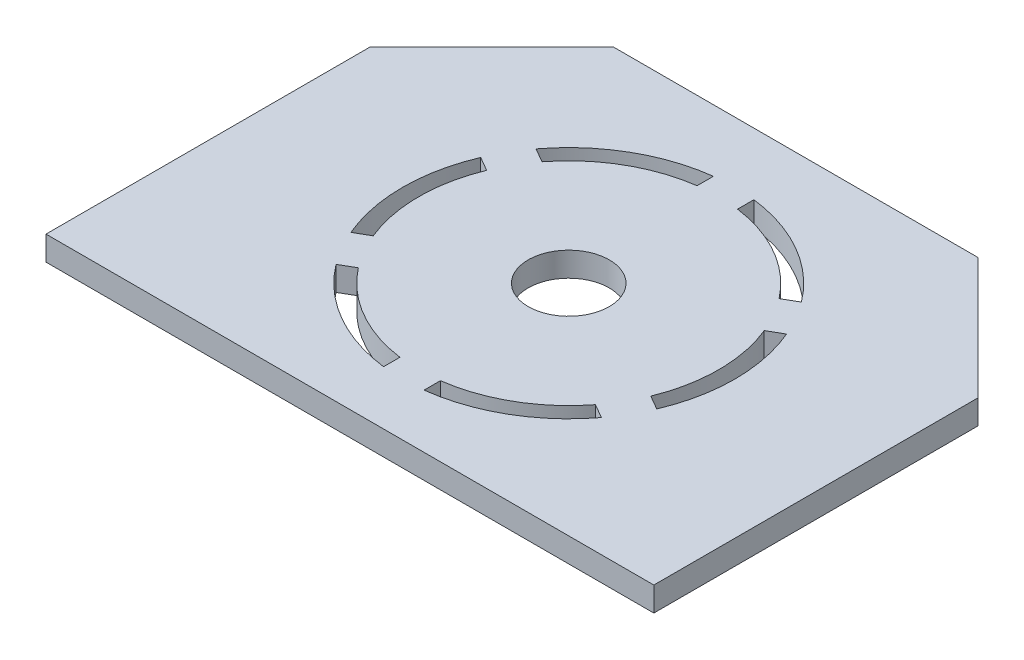
SolidWorks part; units mm, degrees
ref_plane "Front Plane" through (0, 0, 0) normal (0, 0, 1) x (1, 0, 0)
ref_plane "Top Plane" through (0, 0, 0) normal (0, 1, 0) x (1, 0, 0)
ref_plane "Right Plane" through (0, 0, 0) normal (1, 0, 0) x (0, 0, -1)
sketch "Sketch1" plane through (0, 0, 0) normal (0, 1, 0) x (1, 0, 0)
  line L0 (-16.9317, 39.1553) -> (-1.9317, 54.1553)
  line L1 (-1.9317, 54.1553) -> (43.0683, 54.1553)
  line L2 (-16.9317, 39.1553) -> (-16.9317, -0.8447)
  line L3 (-16.9317, -0.8447) -> (58.0683, -0.8447)
  line L4 (58.0683, 39.1553) -> (58.0683, -0.8447)
  line L5 (43.0683, 54.1553) -> (58.0683, 39.1553)
  circle A0 centre (20.5683, 26.1553) radius 5
  circle A1 centre (20.5683, 26.1553) radius 18.5
  circle A2 centre (20.5683, 26.1553) radius 20.5
  point P0 (-16.9317, 54.1553)
  point P3 (58.0683, 54.1553)
  dimension "D3" = 10
  dimension "D4" = 37
  dimension "D1" = 75
  dimension "D2" = 55
  dimension "D6" = 37.5
  dimension "D7" = 27
  dimension "D5" = 2
extrude "Boss-Extrude1" add sketch "Sketch1" along normal blind 3 contours A1 A0 | L4 L1 L2 L3 A2
sketch "Sketch2" plane through (0, 3, 0) normal (0, 1, 0) x (1, 0, 0)
  line L0 (20.5683, 31.1903) -> (20.5683, 28.1237) construction
  line L1 (15.5333, 26.1553) -> (18.6298, 26.1553) construction
  line L2 (18.0683, 44.4856) -> (18.0683, 46.5023)
  line L3 (35.1928, 37.4855) -> (36.9393, 38.4938)
  line L4 (37.6928, 33.1554) -> (39.4393, 34.1637)
  line L5 (37.6928, 19.1552) -> (39.4393, 18.1469)
  line L6 (23.0683, 44.4856) -> (23.0683, 46.5023)
  line L7 (35.1928, 14.8251) -> (36.9393, 13.8167)
  line L8 (23.0683, 7.825) -> (23.0683, 5.8083)
  line L9 (18.0683, 7.825) -> (18.0683, 5.8083)
  line L10 (5.9438, 14.8251) -> (4.1972, 13.8167)
  line L11 (3.4438, 19.1552) -> (1.6972, 18.1469)
  line L12 (3.4438, 33.1554) -> (1.6972, 34.1637)
  line L13 (5.9438, 37.4855) -> (4.1972, 38.4938)
  arc A0 (37.6928, 33.1554) -> (35.1928, 37.4855) centre (20.5683, 26.1553) ccw
  arc A1 (23.0683, 44.4856) -> (18.0683, 44.4856) centre (20.5683, 26.1553) ccw
  arc A2 (23.0683, 46.5023) -> (18.0683, 46.5023) centre (20.5683, 26.1553) ccw
  arc A3 (39.4393, 34.1637) -> (36.9393, 38.4938) centre (20.5683, 26.1553) ccw
  arc A4 (35.1928, 14.8251) -> (37.6928, 19.1552) centre (20.5683, 26.1553) ccw
  arc A5 (36.9393, 13.8167) -> (39.4393, 18.1469) centre (20.5683, 26.1553) ccw
  arc A6 (18.0683, 7.825) -> (23.0683, 7.825) centre (20.5683, 26.1553) ccw
  arc A7 (18.0683, 5.8083) -> (23.0683, 5.8083) centre (20.5683, 26.1553) ccw
  arc A8 (3.4438, 19.1552) -> (5.9438, 14.8251) centre (20.5683, 26.1553) ccw
  arc A9 (1.6972, 18.1469) -> (4.1972, 13.8167) centre (20.5683, 26.1553) ccw
  arc A10 (5.9438, 37.4855) -> (3.4438, 33.1554) centre (20.5683, 26.1553) ccw
  arc A11 (4.1972, 38.4938) -> (1.6972, 34.1637) centre (20.5683, 26.1553) ccw
  point P32 (20.5683, 26.1553)
  dimension "D1" = 6
extrude "Boss-Extrude2" add sketch "Sketch2" against normal through all
